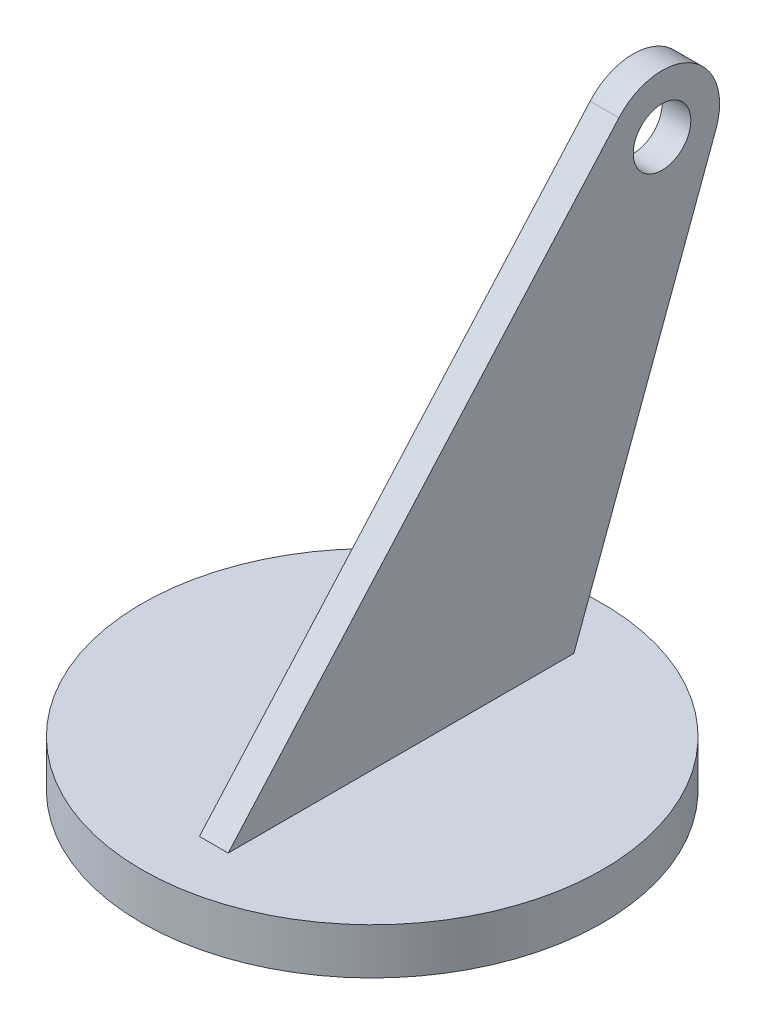
SolidWorks part; units mm, degrees
ref_plane "Front Plane" through (0, 0, 0) normal (0, 0, 1) x (1, 0, 0)
ref_plane "Top Plane" through (0, 0, 0) normal (0, 1, 0) x (1, 0, 0)
ref_plane "Right Plane" through (0, 0, 0) normal (1, 0, 0) x (0, 0, -1)
sketch "Sketch1" plane through (0, 0, 0) normal (0, 1, 0) x (1, 0, 0)
  circle A0 centre (0, 0) radius 40
  dimension "D1" = 80
extrude "Boss-Extrude1" add sketch "Sketch1" along normal mid plane 8
ref_plane "Plane2" through (15, 0, 0) normal (1, 0, 0) x (0, 0, -1)
sketch "Sketch8" plane through (0, 0, 0) normal (1, 0, 0) x (0, 0, -1)
  line L0 (0, 0) -> (0, 4) construction
  line L1 (40, 4) -> (-40, 4) construction
  line L2 (0, 4) -> (-30, 4)
  line L3 (0, 4) -> (30, 4)
  line L4 (30, 4) -> (54.6879, 70.5206)
  line L5 (-30, 4) -> (37.8246, 80.6278)
  arc A0 (54.6879, 70.5206) -> (37.8246, 80.6278) centre (45.3127, 74) ccw
  circle A1 centre (45.3127, 74) radius 5
  dimension "D3" = 20
  dimension "D4" = 10
  dimension "D5" = 70
  dimension "D1" = 30
  dimension "D2" = 30
  dimension "D6" = 102.8202
extrude "Boss-Extrude3" add sketch "Sketch8" along normal blind 5
